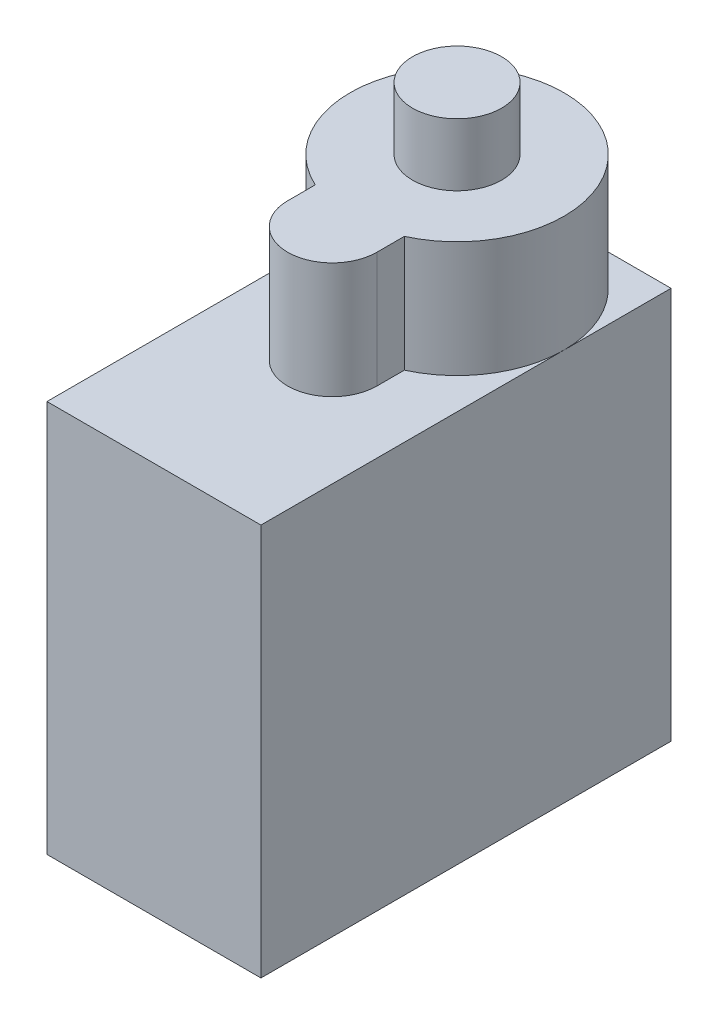
SolidWorks part; units mm, degrees
ref_plane "Front Plane" through (0, 0, 0) normal (0, 0, 1) x (1, 0, 0)
ref_plane "Top Plane" through (0, 0, 0) normal (0, 1, 0) x (1, 0, 0)
ref_plane "Right Plane" through (0, 0, 0) normal (1, 0, 0) x (0, 0, -1)
sketch "Sketch1" plane through (0, 0, 0) normal (0, 1, 0) x (1, 0, 0)
  line L1 (45.3144, -93.1516) -> (57.3144, -93.1516)
  line L2 (45.3144, -93.1516) -> (45.3144, -116.1516)
  line L3 (45.3144, -116.1516) -> (57.3144, -116.1516)
  line L4 (57.3144, -93.1516) -> (57.3144, -116.1516)
  dimension "D1" = 23
  dimension "D2" = 12
sketch "Sketch3" plane through (0, 0, 0) normal (0, 1, 0) x (1, 0, 0)
  line L0 (45.3144, -93.1516) -> (57.3144, -93.1516) construction
  line L1 (57.3144, -93.1516) -> (57.3144, -116.1516) construction
  line L2 (45.3144, -93.1516) -> (45.3144, -116.1516) construction
  line L5 (48.8144, -106.1516) -> (48.8144, -104.606)
  line L6 (53.8144, -104.606) -> (53.8144, -106.1516)
  arc A0 (53.8144, -104.606) -> (48.8144, -104.606) centre (51.3144, -99.1516) ccw
  arc A1 (48.8144, -106.1516) -> (53.8144, -106.1516) centre (51.3144, -106.1516) ccw
  dimension "D1" = 12
  dimension "D4" = 5
  dimension "D2" = 6
  dimension "D3" = 6
  dimension "D5" = 6
  dimension "D6" = 13
sketch "Sketch4" plane through (0, 0, 0) normal (0, 1, 0) x (1, 0, 0)
  line L0 (57.3144, -93.1516) -> (57.3144, -116.1516) construction
  line L1 (45.3144, -93.1516) -> (57.3144, -93.1516) construction
  circle A0 centre (51.3144, -99.1516) radius 2.5
  dimension "D3" = 5
  dimension "D1" = 6
  dimension "D2" = 6
extrude "Boss-Extrude2" add sketch "Sketch4" along normal blind 32
extrude "Boss-Extrude3" add sketch "Sketch3" along normal blind 28.5
extrude "Boss-Extrude4" add sketch "Sketch1" along normal blind 22
sketch "Sketch5" plane through (0, 0, 0) normal (0, 1, 0) x (1, 0, 0)
  line L0 (57.3144, -116.1516) -> (57.3144, -93.1516) construction
  line L1 (57.3144, -93.1516) -> (45.3144, -93.1516) construction
  line L3 (48.8144, -106.1516) -> (48.8144, -104.606)
  line L4 (53.8144, -106.1516) -> (53.8144, -104.606)
  arc A0 (48.8144, -106.1516) -> (53.8144, -106.1516) centre (51.3144, -106.1516) ccw
  circle A1 centre (51.3144, -99.1516) radius 6 construction
  arc A2 (48.8144, -104.606) -> (53.8144, -104.606) centre (51.3144, -99.1516) ccw
  dimension "D1" = 5
  dimension "D2" = 6
  dimension "D3" = 13
